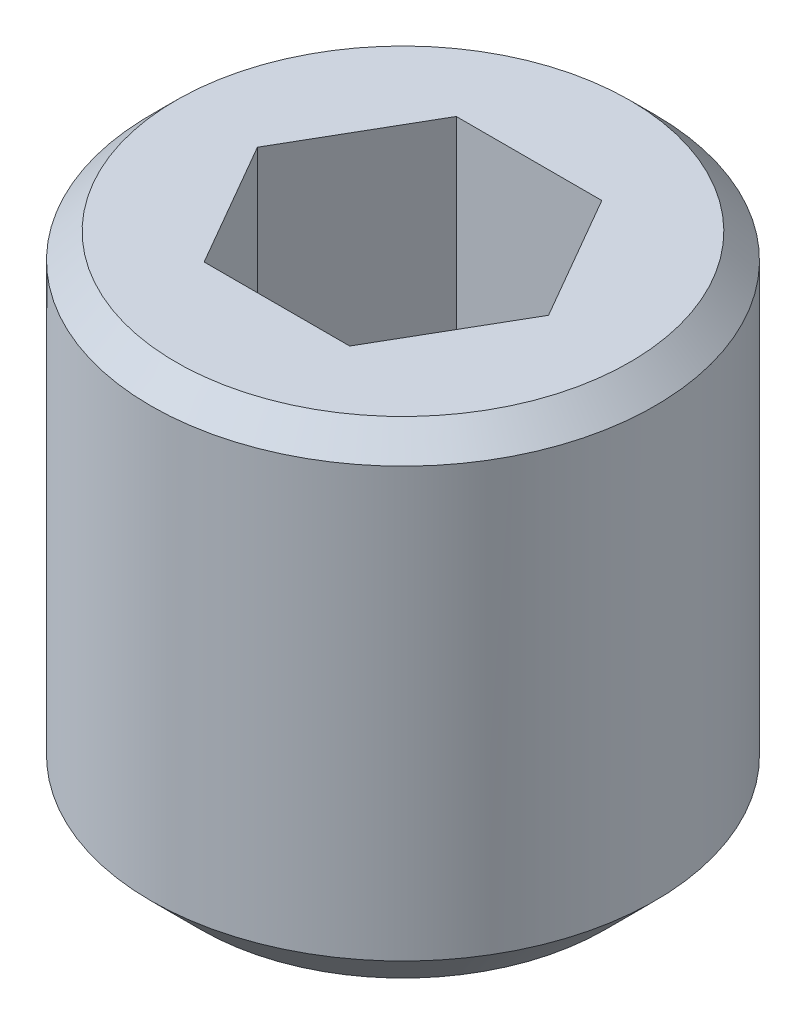
SolidWorks part; units mm, degrees
material "acero"
ref_plane "Alzado" through (0, 0, 0) normal (0, 0, 1) x (1, 0, 0)
ref_plane "Planta" through (0, 0, 0) normal (0, 1, 0) x (1, 0, 0)
ref_plane "Vista lateral" through (0, 0, 0) normal (1, 0, 0) x (0, 0, -1)
sketch "Croquis1" plane through (0, 0, 0) normal (0, 0, 1) x (1, 0, 0)
  line L0 (0, 0) -> (0, -60.9498) construction
  line L1 (0, 0) -> (1.5, 0)
  line L4 (1.5, 0) -> (1.5, -3)
  line L5 (1.5, -3) -> (0, -3)
  line L6 (0, -3) -> (0, 0)
  dimension "D1" = 3
  dimension "D4" = 3
revolve "Revolución1" add sketch "Croquis1" angle 360 about L0
cosmetic thread "Rosca cosmética1" parameters "D2"=2.439
sketch "Croquis3" plane through (0, 0, 0) normal (0, 1, 0) x (1, 0, 0)
  line L1 (-0.433, 0.75) -> (-0.866, 0)
  line L2 (-0.866, 0) -> (-0.433, -0.75)
  line L3 (-0.433, -0.75) -> (0.433, -0.75)
  line L4 (0.433, -0.75) -> (0.866, 0)
  line L5 (0.866, 0) -> (0.433, 0.75)
  line L6 (0.433, 0.75) -> (-0.433, 0.75)
  circle A0 centre (0, 0) radius 0.75 construction
  dimension "D1" = 1.5
extrude "Cortar-Extruir2" cut sketch "Croquis3" against normal blind 1.5
chamfer "Chaflán3" distance 0.3 angle 45
chamfer "Chaflán4" distance 0.15 angle 45
